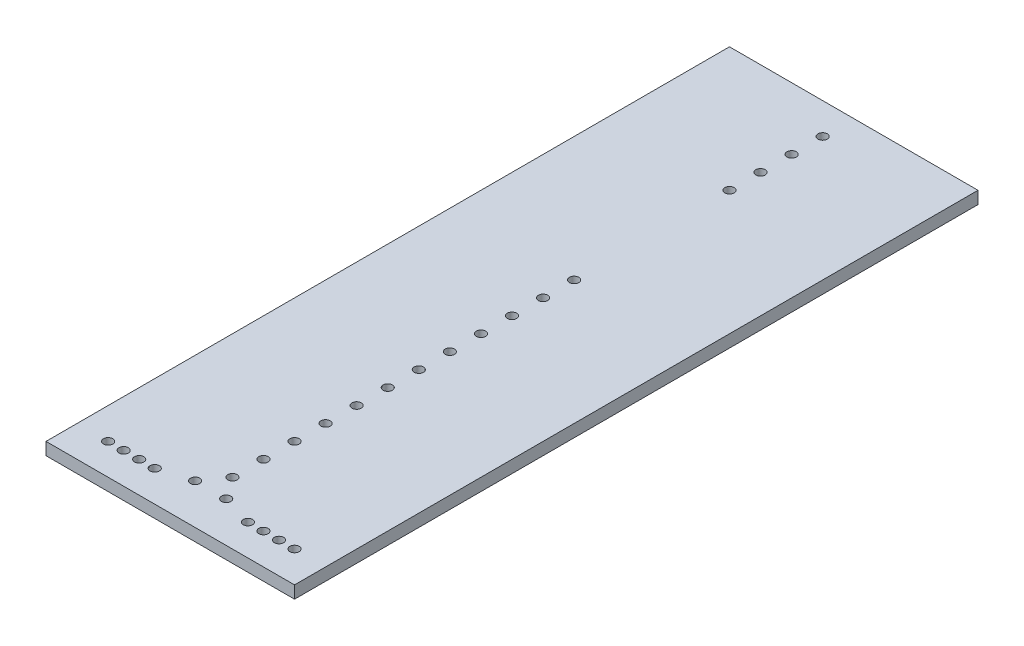
SolidWorks part; units mm, degrees
ref_plane "Front Plane" through (0, 0, 0) normal (0, 0, 1) x (1, 0, 0)
ref_plane "Top Plane" through (0, 0, 0) normal (0, 1, 0) x (1, 0, 0)
ref_plane "Right Plane" through (0, 0, 0) normal (1, 0, 0) x (0, 0, -1)
sketch "Sketch2" plane through (0, 0, 0) normal (0, 1, 0) x (1, 0, 0)
  line L1 (-40, -110) -> (40, -110)
  line L2 (-40, -110) -> (-40, 110)
  line L3 (-40, 110) -> (40, 110)
  line L4 (40, -110) -> (40, 110)
  line L5 (-40, -110) -> (40, 110) construction
  line L6 (-40, 110) -> (40, -110) construction
  point P0 (0, 0)
  dimension "D1" = 80
  dimension "D2" = 220
extrude "main_plate" add sketch "Sketch2" along normal blind 4
sketch "Sketch3" plane through (0, 4, 0) normal (0, 1, 0) x (1, 0, 0)
  line L0 (0, 124.2125) -> (0, -124.2125) construction
  line L1 (-40, -110) -> (40, -110) construction
  circle A0 centre (30, -100) radius 1.5
  circle A3 centre (25, -100) radius 1.5
  circle A4 centre (20, -100) radius 1.5
  circle A5 centre (15, -100) radius 1.5
  point P4 (0, 0)
  dimension "D1" = 3
  dimension "D3" = 4
  dimension "D2" = 30
  dimension "D7" = 10
extrude "elbow_holes" cut sketch "Sketch3" against normal through all
mirror "elbow_mirror" about plane through (0, 0, 0) normal (1, 0, 0) of "elbow_holes"
sketch "Sketch4" plane through (0, 4, 0) normal (0, 1, 0) x (1, 0, 0)
  line L0 (-40, -110) -> (40, -110) construction
  circle A0 centre (0, -90) radius 1.5
  circle A1 centre (0, -80) radius 1.5
  circle A2 centre (0, -70) radius 1.5
  circle A3 centre (0, -60) radius 1.5
  circle A4 centre (0, -50) radius 1.5
  circle A5 centre (0, -40) radius 1.5
  circle A6 centre (0, -30) radius 1.5
  circle A7 centre (0, -20) radius 1.5
  circle A8 centre (0, -10) radius 1.5
  circle A9 centre (0, 0) radius 1.5
  circle A10 centre (0, 10) radius 1.5
  circle A11 centre (0, 20) radius 1.5
  point P4 (0, 0)
  point P7 (0, -110)
  dimension "D1" = 3
  dimension "D2" = 0
  dimension "D4" = 20
  dimension "D3" = 12
extrude "pin_holes" cut sketch "Sketch4" against normal through all
sketch "Sketch5" plane through (0, 4, 0) normal (0, 1, 0) x (1, 0, 0)
  circle A0 centre (5, -97) radius 1.5
  circle A1 centre (15, -100) radius 1.5 construction
  point P4 (0, 0)
  dimension "D1" = 3
  dimension "D2" = 3
  dimension "D3" = 10
extrude "stopper_holes" cut sketch "Sketch5" against normal through all contours A0
mirror "stopper_mirror" about plane through (0, 0, 0) normal (1, 0, 0) of "stopper_holes"
sketch "Sketch6" plane through (0, 4, 0) normal (0, 1, 0) x (1, 0, 0)
  line L0 (40, 110) -> (-40, 110) construction
  circle A0 centre (0, 70) radius 1.5
  circle A1 centre (0, 80) radius 1.5
  circle A2 centre (0, 90) radius 1.5
  circle A3 centre (0, 100) radius 1.5
  point P4 (0, 110)
  dimension "D1" = 3
  dimension "D2" = 0
  dimension "D3" = 40
  dimension "D4" = 4
extrude "spool_holes" cut sketch "Sketch6" against normal through all
